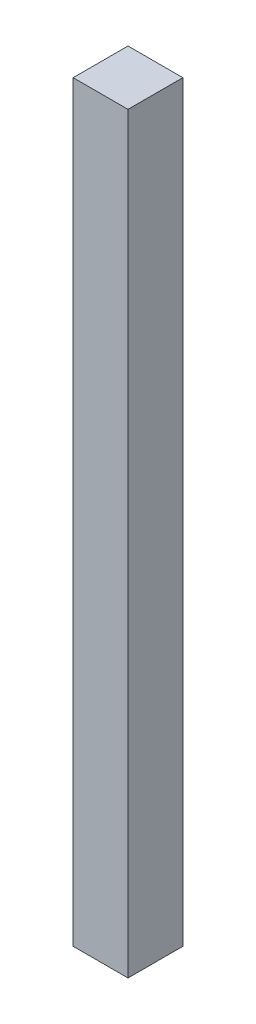
SolidWorks part; units mm, degrees
ref_plane "Front Plane" through (0, 0, 0) normal (0, 0, 1) x (1, 0, 0)
ref_plane "Top Plane" through (0, 0, 0) normal (0, 1, 0) x (1, 0, 0)
ref_plane "Right Plane" through (0, 0, 0) normal (1, 0, 0) x (0, 0, -1)
sketch "Sketch2" plane through (0, 0, 0) normal (0, 1, 0) x (1, 0, 0)
  line L0 (0, 0) -> (-88.9, 0)
  line L1 (-88.9, 0) -> (-88.9, -88.9)
  line L2 (-88.9, -88.9) -> (0, -88.9)
  line L3 (0, -88.9) -> (0, 0)
  dimension "D1" = 88.9
  dimension "D2" = 88.9
extrude "Boss-Extrude1" add sketch "Sketch2" against normal blind 1219.2
